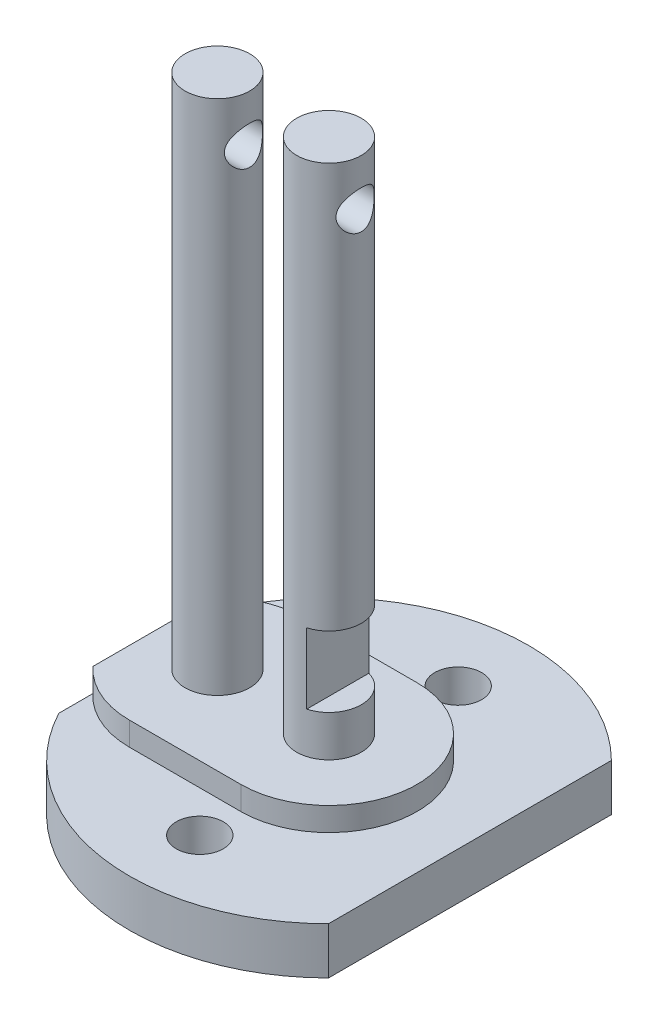
SolidWorks part; units mm, degrees
ref_plane "Front Plane" through (0, 0, 0) normal (0, 0, 1) x (1, 0, 0)
ref_plane "Top Plane" through (0, 0, 0) normal (0, 1, 0) x (1, 0, 0)
ref_plane "Right Plane" through (0, 0, 0) normal (1, 0, 0) x (0, 0, -1)
sketch "Sketch1" plane through (0, 0, 0) normal (0, 1, 0) x (1, 0, 0)
  line L0 (-15, 8) -> (-15, -8)
  line L1 (12, 12.0416) -> (12, -12.0416)
  arc A0 (-15, -8) -> (12, -12.0416) centre (0, 0) ccw
  arc A1 (12, 12.0416) -> (-15, 8) centre (0, 0) ccw
  dimension "D1" = 34
  dimension "D2" = 15
  dimension "D3" = 12
extrude "Boss-Extrude1" add sketch "Sketch1" along normal blind 4
sketch "Sketch2" plane through (0, 0, 0) normal (0, 1, 0) x (1, 0, 0)
  circle A0 centre (0, 0) radius 2.75
  dimension "D1" = 5.5
extrude "Boss-Extrude2" add sketch "Sketch2" along normal blind 50
sketch "Sketch3" plane through (0, 0, 0) normal (0, 0, 1) x (1, 0, 0)
  line L0 (2.75, 4) -> (2.75, 50) construction
  line L1 (2.75, 15.5) -> (0.75, 15.5)
  line L2 (2.75, 15.5) -> (2.75, 9.5)
  line L3 (2.75, 9.5) -> (0.75, 9.5)
  line L4 (0.75, 15.5) -> (0.75, 9.5)
  dimension "D1" = 2
  dimension "D2" = 6
  dimension "D3" = 9.5
extrude "Cut-Extrude1" cut sketch "Sketch3" along normal through all both and the other way through all
sketch "Sketch4" plane through (0, 0, 0) normal (0, 1, 0) x (1, 0, 0)
  line L0 (0, 0) -> (-9.5, 0) construction
  line L1 (0, -7.5) -> (-9.5, -7.5)
  line L2 (0, 7.5) -> (-9.5, 7.5)
  line L3 (-15, 5.099) -> (-15, -5.099)
  line L4 (-15, 8) -> (-15, -8) construction
  arc A1 (0, -7.5) -> (0, 7.5) centre (0, 0) ccw
  arc A2 (-9.5, 7.5) -> (-15, 5.099) centre (-9.5, 0) ccw
  arc A3 (-15, -5.099) -> (-9.5, -7.5) centre (-9.5, 0) ccw
  point P5 (-4.75, 0)
  dimension "D1" = 7.5
  dimension "D2" = 9.5
extrude "Boss-Extrude3" add sketch "Sketch4" along normal blind 6
sketch "Sketch7" plane through (0, 0, 0) normal (0, 1, 0) x (1, 0, 0)
  line L0 (0, 11) -> (0, 0) construction
  line L2 (-16.5, 0) -> (16.5, 0) construction
  circle A0 centre (0, 11) radius 2
  circle A2 centre (0, -11) radius 2
  dimension "D1" = 4
  dimension "D2" = 11
extrude "Cut-Extrude3" cut sketch "Sketch7" along normal blind 10
sketch "Sketch8" plane through (0, 0, 0) normal (0, 1, 0) x (1, 0, 0)
  line L0 (-9.5, 0) -> (0, 0) construction
  circle A0 centre (-9.5, 0) radius 2.75
  dimension "D1" = 5.5
  dimension "D2" = 9.5
extrude "Boss-Extrude4" add sketch "Sketch8" along normal blind 50
sketch "Sketch6" plane through (0, 0, 0) normal (1, 0, 0) x (0, 0, -1)
  line L1 (0, 46) -> (0, 0) construction
  circle A0 centre (0, 46) radius 1.625
  dimension "D1" = 46
  dimension "D2" = 3.25
extrude "Cut-Extrude2" cut sketch "Sketch6" along normal through all both and the other way through all
